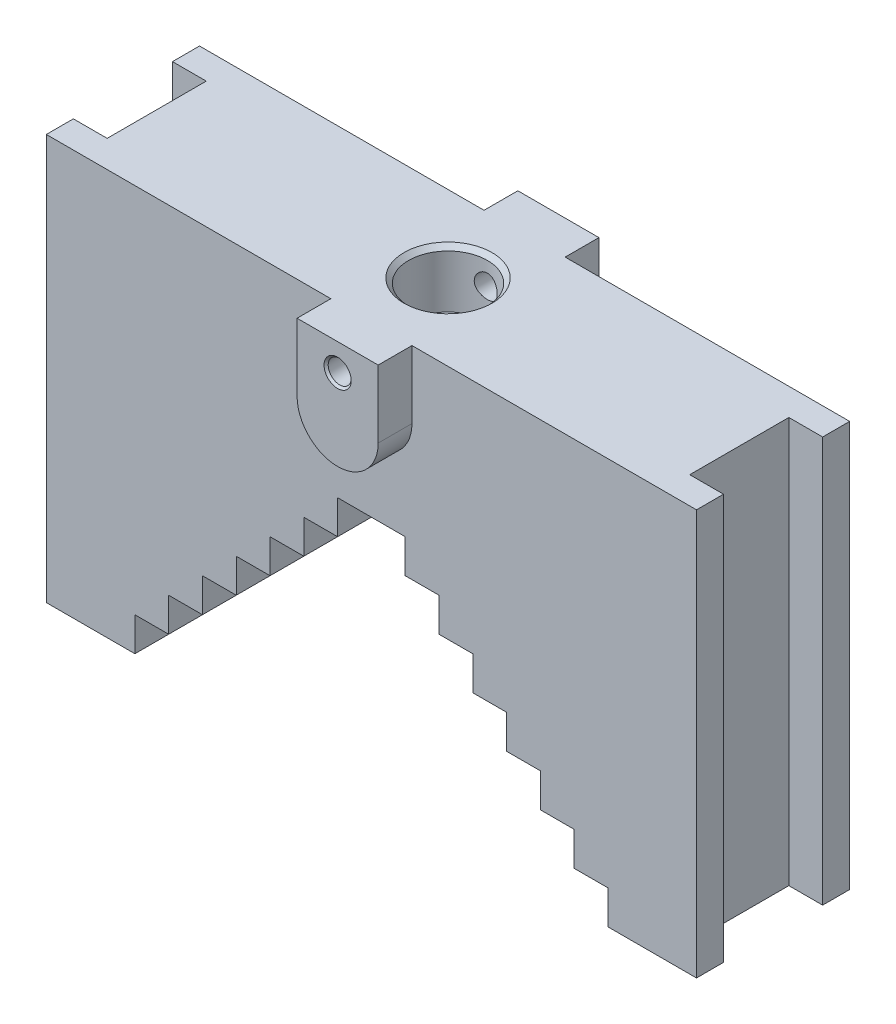
SolidWorks part; units mm, degrees
ref_plane "Front Plane" through (0, 0, 0) normal (0, 0, 1) x (1, 0, 0)
ref_plane "Top Plane" through (0, 0, 0) normal (0, 1, 0) x (1, 0, 0)
ref_plane "Right Plane" through (0, 0, 0) normal (1, 0, 0) x (0, 0, -1)
sketch "Sketch1" plane through (0, 0, 0) normal (0, 0, 1) x (1, 0, 0)
  line L1 (144.315, -90) -> (-144.315, -90)
  line L2 (144.315, -90) -> (144.315, 90)
  line L3 (144.315, 90) -> (-144.315, 90)
  line L4 (-144.315, -90) -> (-144.315, 90)
  line L5 (144.315, -90) -> (-144.315, 90) construction
  line L6 (144.315, 90) -> (-144.315, -90) construction
  line L8 (0, 91.6649) -> (0, -113.2548) construction
  line L9 (0, -55) -> (0, 55) construction
  point P0 (0, 0)
  dimension "D1" = 288.63
  dimension "D2" = 180
extrude "Boss-Extrude1" add sketch "Sketch1" along normal blind 68
sketch "Sketch3" plane through (0, 0, 68) normal (0, 0, 1) x (1, 0, 0)
  line L0 (15, 15) -> (-15, 15)
  line L1 (0, -55) -> (0, 55) construction
  line L2 (-15, 15) -> (-15, 0)
  line L3 (-15, 0) -> (-30, 0)
  line L4 (-30, 0) -> (-30, -15)
  line L5 (-30, -15) -> (-45, -15)
  line L6 (-45, -15) -> (-45, -30)
  line L7 (-45, -30) -> (-60, -30)
  line L8 (-60, -30) -> (-60, -45)
  line L9 (-60, -45) -> (-75, -45)
  line L10 (-75, -45) -> (-75, -60)
  line L11 (-75, -60) -> (-90, -60)
  line L12 (-90, -60) -> (-90, -75)
  line L13 (-90, -75) -> (-105, -75)
  line L14 (-105, -75) -> (-105, -90)
  line L15 (-144.315, -90) -> (144.315, -90) construction
  line L16 (0, 104.2406) -> (0, -111.7821) construction
  line L17 (105, -75) -> (105, -90)
  line L18 (90, -75) -> (105, -75)
  line L19 (90, -60) -> (90, -75)
  line L20 (75, -60) -> (90, -60)
  line L21 (75, -45) -> (75, -60)
  line L22 (60, -45) -> (75, -45)
  line L23 (60, -30) -> (60, -45)
  line L24 (45, -30) -> (60, -30)
  line L25 (45, -15) -> (45, -30)
  line L26 (30, -15) -> (45, -15)
  line L27 (30, 0) -> (30, -15)
  line L28 (15, 0) -> (30, 0)
  line L29 (15, 15) -> (15, 0)
  line L30 (-105, -90) -> (105, -90)
  point P36 (0, 15)
  dimension "D1" = 15
  dimension "D2" = 15
  dimension "D3" = 15
  dimension "D4" = 15
  dimension "D5" = 15
  dimension "D6" = 15
  dimension "D7" = 15
  dimension "D8" = 15
  dimension "D9" = 15
  dimension "D10" = 15
  dimension "D11" = 15
  dimension "D12" = 15
  dimension "D13" = 15
  dimension "D14" = 15
  dimension "D15" = 210
extrude "Cut-Extrude5" cut sketch "Sketch3" against normal through all
sketch "Sketch7" plane through (0, 0, 68) normal (0, 0, 1) x (1, 0, 0)
  line L0 (0, 132.351) -> (0, -135.0764) construction
  line L1 (0, -37.4) -> (0, 37.4) construction
  line L3 (144.315, 90) -> (-144.315, 90) construction
  line L4 (-18, 90) -> (-18, 60)
  line L6 (18, 90) -> (18, 60)
  line L7 (-18, 90) -> (18, 90)
  arc A0 (18, 60) -> (-18, 60) centre (0, 60) cw
  dimension "D4" = 18
  dimension "D1" = 36
  dimension "D3" = 30
extrude "Boss-Extrude2" add sketch "Sketch7" along normal blind 15
sketch "Sketch8" plane through (0, 0, 0) normal (0, 0, -1) x (-1, 0, 0)
  line L0 (-18, 90) -> (18, 90)
  line L1 (18, 90) -> (18, 60)
  line L2 (-18, 90) -> (-18, 60)
  arc A0 (-18, 60) -> (18, 60) centre (0, 60) ccw
  dimension "D2" = 18
  dimension "D1" = 30
  dimension "D3" = 36
extrude "Boss-Extrude3" add sketch "Sketch8" along normal blind 15
sketch "Sketch9" plane through (-144.315, 0, 0) normal (-1, 0, 0) x (0, 0, 1)
  line L0 (34, 109.2894) -> (34, -115.6131) construction
  line L1 (56, 90) -> (12, 90)
  line L2 (68, 90) -> (0, 90) construction
  line L3 (12, 90) -> (12, -90)
  line L4 (68, -90) -> (0, -90) construction
  line L5 (12, -90) -> (56, -90)
  line L7 (56, 90) -> (56, -90)
  point P11 (34, -90)
  point P12 (34, 90)
  dimension "D1" = 22
  dimension "D2" = 180
extrude "Cut-Extrude6" cut sketch "Sketch9" against normal blind 15
sketch "Sketch10" plane through (144.315, 0, 0) normal (1, 0, 0) x (0, 0, -1)
  line L0 (-56, 90) -> (-12, 90)
  line L1 (-12, 90) -> (-12, -90)
  line L2 (-12, -90) -> (-56, -90)
  line L3 (-68, -90) -> (0, -90) construction
  line L4 (-56, -90) -> (-56, 90)
extrude "Cut-Extrude7" cut sketch "Sketch10" against normal blind 15
sketch "Sketch12" plane through (0, 90, 0) normal (0, 1, 0) x (1, 0, 0)
  line L0 (0, 62.5805) -> (0, -126.8331) construction
  line L1 (0, -99) -> (0, 99) construction
hole_wizard "M12 Tapped Hole1" positions "Sketch25" profile "Sketch26" tap size "M12" standard "ISO" end condition up to next
sketch "Sketch25" plane through (0, 0, 83) normal (0, 0, 1) x (1, 0, 0)
  line L0 (0, -99) -> (0, 99) construction
  line L1 (18, 90) -> (-18, 90) construction
  point P0 (0, 78)
  dimension "D1" = 12
sketch "Sketch26" plane through (0, 78, 83) normal (1, 0, 0) x (0, -1, 0)
  line L0 (0, 0) -> (0, 98)
  line L1 (0, 98) -> (5.1, 98)
  line L2 (5.1, 98) -> (5.1, 0.925)
  line L3 (5.1, 0.925) -> (6.025, 0)
  line L5 (6.025, 0) -> (0, 0)
  line L6 (-5.1, 0.925) -> (-6.025, 0) construction
  line L11 (0, -6.35) -> (0, 107.95) construction
  dimension "Thru Tap Drill Dia." = 10.2
  dimension "Thru Tap Drill Depth" = 98
  dimension "Near C'Sink Dia." = 12.05
  dimension "Near C'Sink Angle" = 90
cosmetic thread "Hole Thread2" parameters "D2"=12
hole_wizard "M12 Tapped Hole2" positions "Sketch27" profile "Sketch28" tap size "M12" standard "ISO" end condition up to next
sketch "Sketch27" plane through (0, 0, -15) normal (0, 0, -1) x (-1, 0, 0)
  line L0 (0, 99) -> (0, -99) construction
  line L1 (18, 90) -> (-18, 90) construction
  point P0 (0, 78)
  dimension "D1" = 12
sketch "Sketch28" plane through (0, 78, -15) normal (1, 0, 0) x (0, 1, 0)
  line L0 (0, 0) -> (0, 98)
  line L1 (0, 98) -> (5.1, 98)
  line L2 (5.1, 98) -> (5.1, 0.925)
  line L3 (5.1, 0.925) -> (6.025, 0)
  line L5 (6.025, 0) -> (0, 0)
  line L6 (-5.1, 0.925) -> (-6.025, 0) construction
  line L11 (0, -6.35) -> (0, 107.95) construction
  dimension "Thru Tap Drill Dia." = 10.2
  dimension "Thru Tap Drill Depth" = 98
  dimension "Near C'Sink Dia." = 12.05
  dimension "Near C'Sink Angle" = 90
cosmetic thread "Hole Thread3" parameters "D2"=13.85
hole_wizard "M39 Tapped Hole1" positions "Sketch30" profile "Sketch31" tap size "M39" standard "ISO"
sketch "Sketch30" plane through (0, 90, 0) normal (0, 1, 0) x (1, 0, 0)
  line L0 (-18, 15) -> (18, 15) construction
  line L1 (-129.315, -56) -> (-129.315, -12) construction
  point P0 (0, -34)
  point P5 (0, 15)
  point P8 (-129.315, -34)
  dimension "D1" = 49
  dimension "D2" = 129.315
sketch "Sketch31" plane through (0, 90, 34) normal (1, 0, 0) x (0, 0, 1)
  line L0 (0, 0) -> (0, 36)
  line L1 (0, 36) -> (17.5, 25.4849)
  line L2 (17.5, 25.4849) -> (17.5, 2.025)
  line L3 (17.5, 2.025) -> (19.525, 0)
  line L5 (19.525, 0) -> (0, 0)
  line L6 (-17.5, 2.025) -> (-19.525, 0) construction
  line L10 (0, 36) -> (-17.5, 25.4849) construction
  line L11 (0, -6.35) -> (0, 107.95) construction
  dimension "Tap Drill Dia." = 35
  dimension "Tap Drill Depth" = 36
  dimension "Near C'Sink Dia." = 39.05
  dimension "Near C'Sink Angle" = 90
  dimension "Drill Angle" = 118
cosmetic thread "Hole Thread5" parameters "D1"=1, "D2"=39
